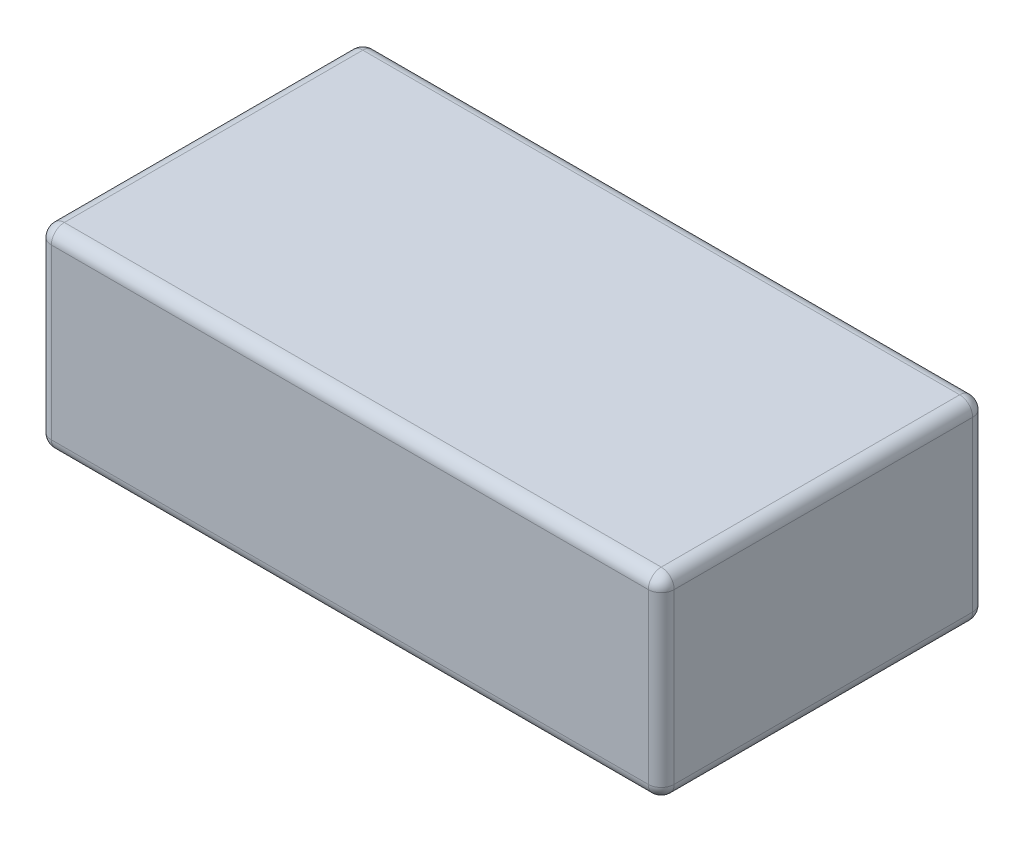
SolidWorks part; units mm, degrees
ref_plane "Front Plane" through (0, 0, 0) normal (0, 0, 1) x (1, 0, 0)
ref_plane "Top Plane" through (0, 0, 0) normal (0, 1, 0) x (1, 0, 0)
ref_plane "Right Plane" through (0, 0, 0) normal (1, 0, 0) x (0, 0, -1)
sketch "Sketch1" plane through (0, 0, 0) normal (0, 1, 0) x (1, 0, 0)
  line L1 (-24, -12.5) -> (24, -12.5)
  line L2 (-24, -12.5) -> (-24, 12.5)
  line L3 (-24, 12.5) -> (24, 12.5)
  line L4 (24, -12.5) -> (24, 12.5)
  line L5 (-24, -12.5) -> (24, 12.5) construction
  line L6 (-24, 12.5) -> (24, -12.5) construction
  point P0 (0, 0)
  dimension "D1" = 25
  dimension "D2" = 48
extrude "Boss-Extrude1" add sketch "Sketch1" along normal blind 15
fillet "Fillet1" radius 1 12 edges at (24, 0, 0) (0, 0, -12.5) (-24, 0, 0) (0, 0, 12.5) (24, 15, 0) (0, 15, -12.5) (-24, 15, 0) (0, 15, 12.5) (24, 7.5, 12.5) (-24, 7.5, 12.5) (24, 7.5, -12.5) (-24, 7.5, -12.5)
